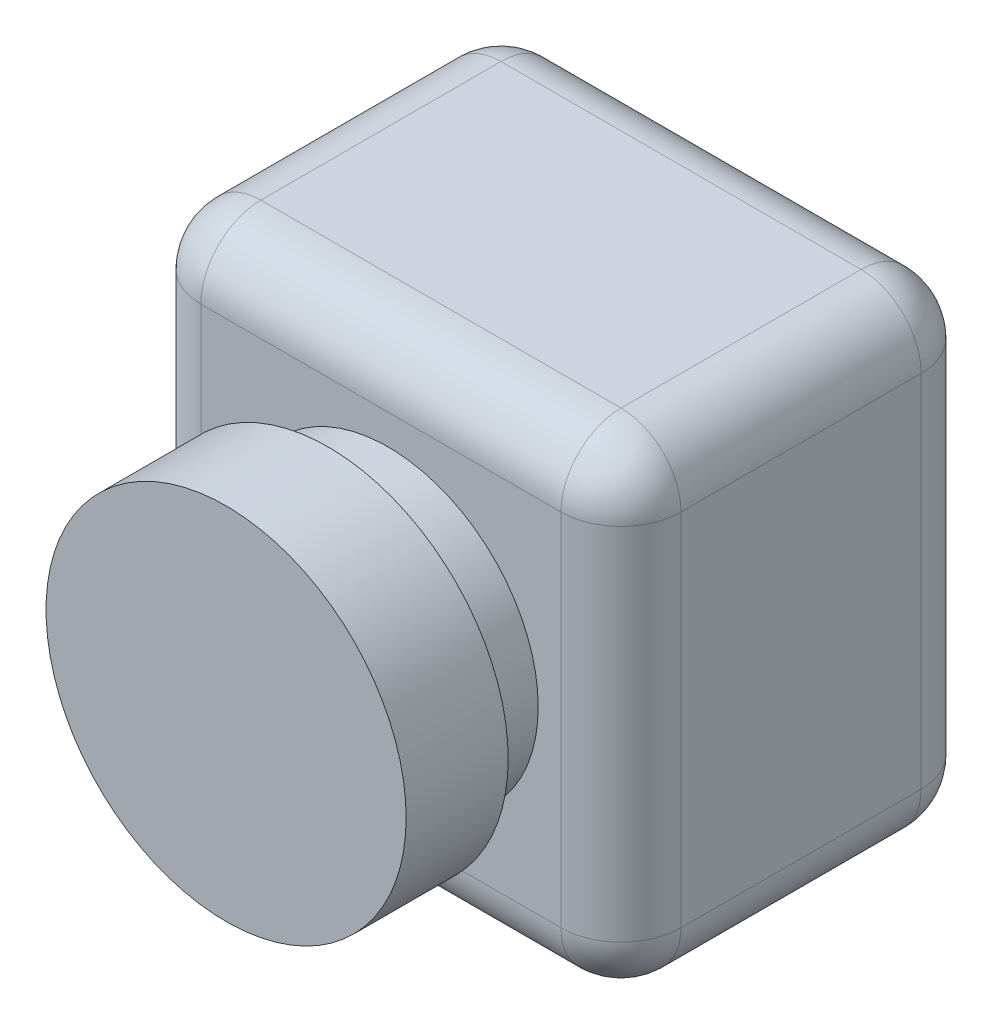
SolidWorks part; units mm, degrees
ref_plane "정면" through (0, 0, 0) normal (0, 0, 1) x (1, 0, 0)
ref_plane "윗면" through (0, 0, 0) normal (0, 1, 0) x (1, 0, 0)
ref_plane "우측면" through (0, 0, 0) normal (1, 0, 0) x (0, 0, -1)
sketch "스케치1" plane through (0, 0, 0) normal (0, 0, 1) x (1, 0, 0)
  line L1 (0, 0) -> (80, 0)
  line L2 (0, 0) -> (0, -80)
  line L3 (0, -80) -> (80, -80)
  line L4 (80, 0) -> (80, -80)
  dimension "D1" = 80
  dimension "D2" = 80
extrude "보스-돌출1" add sketch "스케치1" along normal blind 60
fillet "필렛1" radius 10 12 edges at (40, -80, 60) (40, -80, 0) (0, -40, 60) (0, -80, 30) (0, -40, 0) (40, 0, 60) (0, 0, 30) (40, 0, 0) (80, -80, 30) (80, -40, 60) (80, 0, 30) (80, -40, 0)
sketch "스케치2" plane through (0, 0, 60) normal (0, 0, 1) x (1, 0, 0)
  line L0 (10, -70) -> (70, -70) construction
  circle A0 centre (41.2074, -40) radius 25
  point P2 (0, 0)
  point P5 (0, 0)
  dimension "D2" = 50
  dimension "D1" = 30
extrude "보스-돌출2" add sketch "스케치2" along normal blind 10
sketch "스케치3" plane through (0, 0, 70) normal (0, 0, 1) x (1, 0, 0)
  circle A0 centre (41.2074, -40) radius 30
  dimension "D1" = 60
extrude "보스-돌출3" add sketch "스케치3" along normal blind 17
